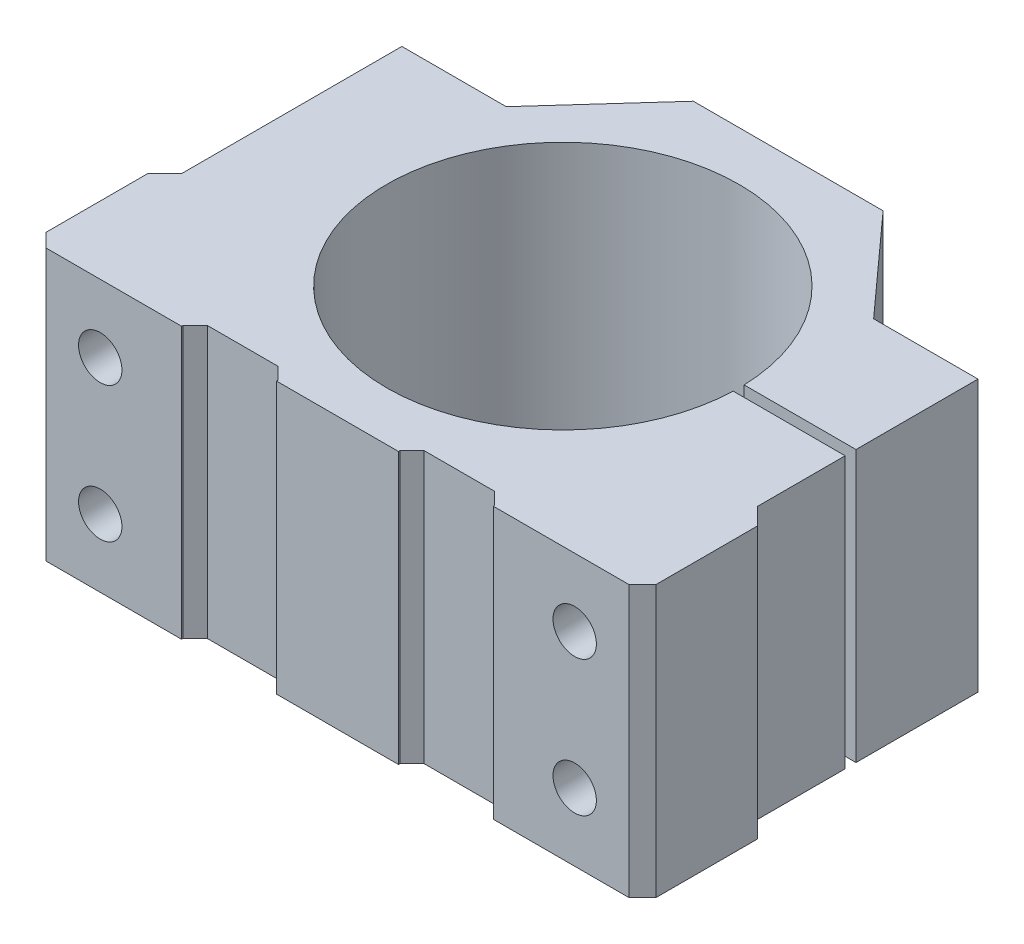
SolidWorks part; units mm, degrees
ref_plane "Alzado" through (0, 0, 0) normal (0, 0, 1) x (1, 0, 0)
ref_plane "Planta" through (0, 0, 0) normal (0, 1, 0) x (1, 0, 0)
ref_plane "Vista lateral" through (0, 0, 0) normal (1, 0, 0) x (0, 0, -1)
sketch "Croquis1" plane through (0, 0, 0) normal (0, 1, 0) x (1, 0, 0)
  line L0 (-42.5, 18.75) -> (-42.5, -13.75)
  line L1 (-45, -33.25) -> (45, -33.25) construction
  line L2 (-45, -33.25) -> (-45, 33.25) construction
  line L3 (-45, 33.25) -> (45, 33.25) construction
  line L4 (45, -33.25) -> (45, 33.25) construction
  line L5 (-45, -33.25) -> (45, 33.25) construction
  line L6 (-45, 33.25) -> (45, -33.25) construction
  line L7 (-14, 33.25) -> (14, 33.25)
  line L8 (0, 33.25) -> (0, -38.2432) construction
  line L9 (-43, -33.25) -> (-45, -31.25)
  line L10 (-43, -33.25) -> (-23, -33.25)
  line L11 (-42.5, 18.75) -> (-27.1, 18.75)
  line L12 (-27.1, 18.75) -> (-14, 33.25)
  line L13 (-45, -31.25) -> (-45, -16.25)
  line L14 (-42.5, -13.75) -> (-45, -16.25)
  line L15 (-23, -33.25) -> (-23, -33.05)
  line L16 (9, -33.25) -> (-9, -33.25)
  line L17 (-9, -33.25) -> (-9, -33.05)
  line L18 (-10.8, -31.25) -> (-21.2, -31.25)
  line L19 (-21.2, -31.25) -> (-23, -33.05)
  line L20 (-9, -33.05) -> (-10.8, -31.25)
  line L21 (9, -33.05) -> (10.8, -31.25)
  line L22 (10.8, -31.25) -> (21.2, -31.25)
  line L23 (21.2, -31.25) -> (23, -33.05)
  line L24 (43, -33.25) -> (23, -33.25)
  line L25 (43, -33.25) -> (45, -31.25)
  line L26 (45, -31.25) -> (45, -16.25)
  line L27 (42.5, -13.75) -> (45, -16.25)
  line L28 (42.5, 18.75) -> (42.5, -13.75)
  line L29 (42.5, 18.75) -> (27.1, 18.75)
  line L30 (27.1, 18.75) -> (14, 33.25)
  line L31 (23, -33.05) -> (23, -33.25)
  line L32 (9, -33.05) -> (9, -33.25)
  circle A0 centre (0, 0) radius 26
  point P15 (-23, -31.25)
  point P21 (-9, -31.25)
  point P26 (0, -33.25)
  dimension "D2" = 52
  dimension "D1" = 66.5
  dimension "D3" = 90
  dimension "D5" = 42.5
  dimension "D7" = 14
  dimension "D8" = 52
  dimension "D9" = 15.4
  dimension "D10" = 32.5
  dimension "D11" = 17
extrude "Saliente-Extruir1" add sketch "Croquis1" along normal blind 40
sketch "Croquis2" plane through (0, 0, -33.25) normal (0, 0, -1) x (-1, 0, 0)
  line L0 (-35, 46.2701) -> (-35, -12.3858) construction
  line L1 (0, 40) -> (0, -7.938) construction
  line L2 (-14, 40) -> (14, 40) construction
  line L11 (-45, 40) -> (-45, 0) construction
  circle A0 centre (-35, 30) radius 3.2
  circle A1 centre (-35, 10) radius 3.2
  circle A2 centre (35, 10) radius 3.2
  circle A3 centre (35, 30) radius 3.2
  point P14 (-45, 20)
  dimension "D2" = 20
  dimension "D4" = 6.4
  dimension "D5" = 6.4
  dimension "D1" = 35
  dimension "D3" = 10
extrude "Cortar-Extruir1" cut sketch "Croquis2" against normal through all
sketch "Croquis3" plane through (42.5, 0, 0) normal (1, 0, 0) x (0, 0, -1)
  line L0 (-13.75, 0) -> (18.75, 0) construction
  line L1 (0.75, 0) -> (-0.85, 0)
  line L2 (0.75, 0) -> (0.75, 40)
  line L3 (0.75, 40) -> (-0.85, 40)
  line L4 (-0.85, 0) -> (-0.85, 40)
  line L5 (-13.75, 40) -> (18.75, 40) construction
  line L6 (18.75, 40) -> (18.75, 0) construction
  dimension "D1" = 1.6
  dimension "D2" = 18
extrude "Cortar-Extruir2" cut sketch "Croquis3" against normal up to next
